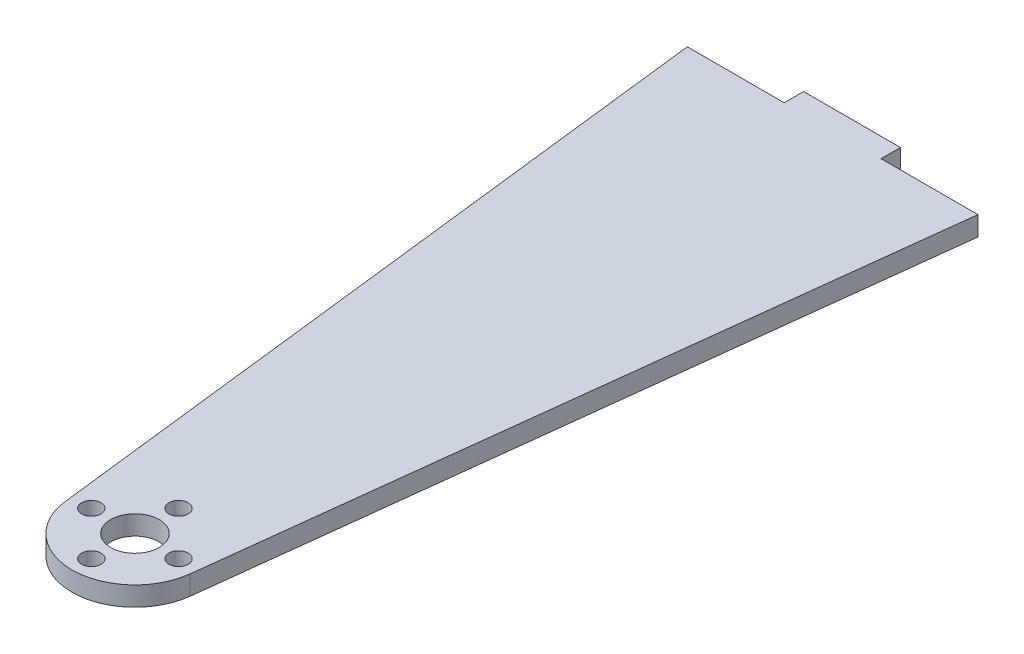
SolidWorks part; units mm, degrees
material "Pine"
ref_plane "Front Plane" through (0, 0, 0) normal (0, 0, 1) x (1, 0, 0)
ref_plane "Top Plane" through (0, 0, 0) normal (0, 1, 0) x (1, 0, 0)
ref_plane "Right Plane" through (0, 0, 0) normal (1, 0, 0) x (0, 0, -1)
sketch "Sketch2" plane through (0, 69.85, 0) normal (0, 1, 0) x (1, 0, 0)
  line L0 (-103.1875, 0) -> (103.1875, 0) construction
  line L1 (-15.875, 6.35) -> (15.875, 6.35)
  line L4 (15.875, 6.35) -> (15.875, 0)
  line L9 (-47.625, 0) -> (-20.4966, -231.007)
  line L10 (-15.875, 0) -> (-47.625, 0)
  line L15 (0, 0) -> (0, -228.6) construction
  line L16 (47.625, 0) -> (15.875, 0)
  line L23 (-15.875, 6.35) -> (-15.875, 0)
  line L24 (47.625, 0) -> (20.4966, -231.007)
  line L26 (-25.4, 0) -> (-9.525, 0) construction
  arc A6 (-20.4966, -231.007) -> (20.4966, -231.007) centre (0, -228.6) ccw
  circle A7 centre (0, -228.6) radius 7.9375
  circle A8 centre (0, -214.3125) radius 3.175
  circle A9 centre (14.2875, -228.6) radius 3.175
  circle A10 centre (0, -242.8875) radius 3.175
  circle A11 centre (-14.2875, -228.6) radius 3.175
  arc A12 (-20.3828, -231.8326) -> (20.3828, -231.8326) centre (0, -228.6) ccw construction
  circle A13 centre (0, -228.6) radius 7.9375 construction
  circle A14 centre (-14.2875, -228.6) radius 3.175 construction
  circle A15 centre (14.2875, -228.6) radius 3.175 construction
  circle A16 centre (0, -242.8875) radius 3.175 construction
  circle A17 centre (0, -214.3125) radius 3.175 construction
  dimension "D1" = 95.25
extrude "Boss-Extrude1" add sketch "Sketch2" along normal blind 6.35
